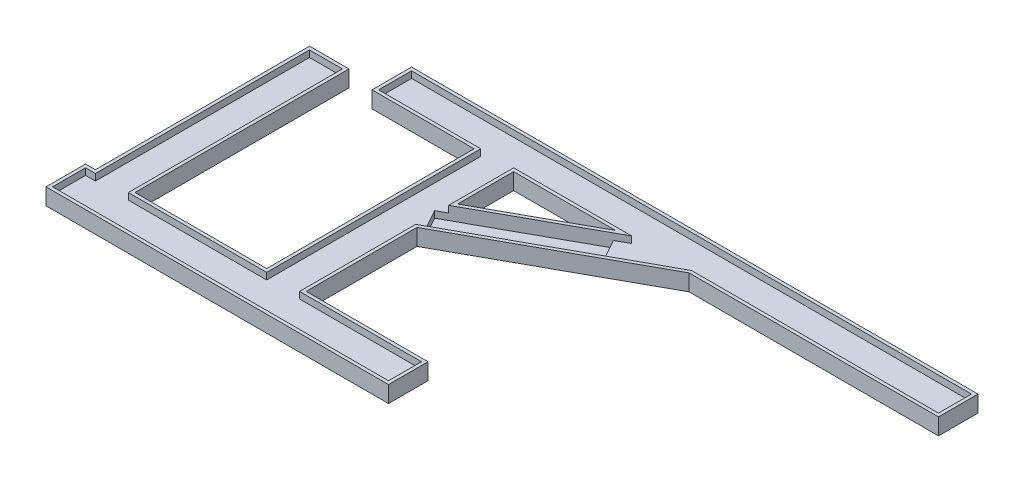
SolidWorks part; units mm, degrees
ref_plane "前视基准面" through (0, 0, 0) normal (0, 0, 1) x (1, 0, 0)
ref_plane "上视基准面" through (0, 0, 0) normal (0, 1, 0) x (1, 0, 0)
ref_plane "右视基准面" through (0, 0, 0) normal (1, 0, 0) x (0, 0, -1)
other "Configuration Table"
sketch "草图1" plane through (0, 0, 0) normal (0, 1, 0) x (1, 0, 0)
  line L0 (0, 0) -> (0, -75) construction
  line L1 (-42.5, -5) -> (42.5, -5)
  line L2 (-42.5, -5) -> (-42.5, 5)
  line L3 (-42.5, 5) -> (42.5, 5)
  line L4 (42.5, -5) -> (42.5, 5)
  line L5 (-42.5, -5) -> (42.5, 5) construction
  line L6 (-42.5, 5) -> (42.5, -5) construction
  line L7 (-25.5, -80) -> (25.5, -80)
  line L8 (-25.5, -80) -> (-25.5, -70)
  line L9 (-25.5, -70) -> (25.5, -70)
  line L10 (25.5, -80) -> (25.5, -70)
  line L11 (-25.5, -80) -> (25.5, -70) construction
  line L12 (-25.5, -70) -> (25.5, -80) construction
  line L13 (-11.5, -70) -> (-21.5, -70)
  line L18 (-11.5, -70) -> (-11.5, -5)
  line L19 (-11.5, -5) -> (-21.5, -5)
  line L20 (-21.5, -70) -> (-21.5, -5)
  line L21 (-11.5, -70) -> (-21.5, -5) construction
  line L22 (-11.5, -5) -> (-21.5, -70) construction
  line L28 (-76.5, -80) -> (-25.5, -80)
  line L33 (-76.5, -80) -> (-76.5, -70)
  line L35 (-16.5, -37.5) -> (-16.5, -32.5) construction
  line L44 (-16.5, -32.5) -> (42.5, 0)
  line L45 (-16.5, -37.5) -> (42.5, -5)
  line L46 (42.5, 5) -> (-16.5, -27.5)
  line L47 (-16.5, -27.5) -> (-16.5, -32.5)
  line L51 (-76.5, -70) -> (-25.5, -70)
  line L52 (-25.5, -80) -> (-25.5, -70)
  line L53 (-73.5, -70) -> (-63.5, -70)
  line L54 (-73.5, -70) -> (-73.5, -5)
  line L55 (-73.5, -5) -> (-63.5, -5)
  line L56 (-63.5, -70) -> (-63.5, -5)
  line L57 (-73.5, -70) -> (-63.5, -5) construction
  line L58 (-73.5, -5) -> (-63.5, -70) construction
  line L59 (-76.5, -80) -> (-25.5, -70) construction
  line L60 (-76.5, -70) -> (-25.5, -80) construction
  line L65 (127.5, -5) -> (42.5, -5)
  line L66 (127.5, -5) -> (127.5, 5)
  line L67 (127.5, 5) -> (42.5, 5)
  line L68 (42.5, -5) -> (42.5, 5)
  line L69 (127.5, -5) -> (42.5, 5) construction
  line L70 (127.5, 5) -> (42.5, -5) construction
  point P0 (0, 0)
  point P6 (0, -75)
  point P11 (-16.5, -37.5)
  point P16 (85, 0)
  point P17 (-68.5, -37.5)
  point P21 (-51, -75)
  point P26 (5.3976, -20.4378)
  dimension "D1" = 10
  dimension "D2" = 85
  dimension "D3" = 51
  dimension "D4" = 10
  dimension "D5" = 10
  dimension "D6" = 65
  dimension "D7" = 4
  dimension "D8" = 51
  dimension "D9" = 21
  dimension "D10" = 5
  dimension "D11" = 25
  dimension "D12" = 65
  dimension "D13" = 85
  dimension "D14" = 10
sketch "草图3" plane through (0, 0, 0) normal (0, 1, 0) x (1, 0, 0)
  line L0 (42.5, -5) -> (42.5, 5)
  line L1 (-73.5, -5) -> (-63.5, -5)
  line L2 (-73.5, -5) -> (-73.5, -70)
  line L3 (-73.5, -70) -> (-63.5, -70)
  line L4 (-63.5, -5) -> (-63.5, -70)
  line L5 (-76.5, -80) -> (25.5, -80)
  line L6 (-76.5, -80) -> (-76.5, -70)
  line L7 (-76.5, -70) -> (25.5, -70)
  line L8 (25.5, -80) -> (25.5, -70)
  line L9 (-21.5, -5) -> (-11.5, -5)
  line L10 (-21.5, -5) -> (-21.5, -70)
  line L11 (-21.5, -70) -> (-11.5, -70)
  line L12 (-11.5, -5) -> (-11.5, -70)
  line L13 (-42.5, 5) -> (127.5, 5)
  line L14 (-42.5, 5) -> (-42.5, -5)
  line L15 (-42.5, -5) -> (127.5, -5)
  line L16 (127.5, 5) -> (127.5, -5)
  line L17 (42.5, -5) -> (-16.5, -37.5)
  line L18 (42.5, 5) -> (-16.5, -27.5)
  line L19 (-16.5, -37.5) -> (-16.5, -27.5)
extrude "凸台-拉伸2" add sketch "草图3" along normal blind 1 contours L4 L1 L2 L3 | L5 L8 L7 L3 L6 | L17 L19 L18 L12 L9 L10 L7 | L18 L13 L14 L15 L9 | L16 L13 L0 L15 | L0 L18 L15 | L15 L18 L12 L17 | L19 L17 L12 L18
sketch "草图4" plane through (0, 1, 0) normal (0, 1, 0) x (1, 0, 0)
  line L0 (-10.5, -35.3366) -> (42.7572, -6)
  line L1 (42.7572, -6) -> (128.5, -6)
  line L2 (128.5, -6) -> (128.5, 6)
  line L3 (128.5, 6) -> (-43.5, 6)
  line L4 (-43.5, 6) -> (-43.5, -6)
  line L5 (-43.5, -6) -> (-22.5, -6)
  line L6 (-22.5, -6) -> (-22.5, -69)
  line L7 (-22.5, -69) -> (-62.5, -69)
  line L8 (-62.5, -69) -> (-62.5, -4)
  line L9 (-62.5, -4) -> (-74.5, -4)
  line L10 (-74.5, -4) -> (-74.5, -69)
  line L11 (-74.5, -69) -> (-77.5, -69)
  line L12 (-77.5, -69) -> (-77.5, -81)
  line L13 (-77.5, -81) -> (26.5, -81)
  line L14 (26.5, -81) -> (26.5, -69)
  line L15 (26.5, -69) -> (-10.5, -69)
  line L16 (-10.5, -69) -> (-10.5, -35.3366)
  line L17 (-11.5, -34.7458) -> (42.5, -5)
  line L18 (42.5, -5) -> (127.5, -5)
  line L19 (127.5, -5) -> (127.5, 5)
  line L20 (127.5, 5) -> (-42.5, 5)
  line L21 (-42.5, 5) -> (-42.5, -5)
  line L22 (-42.5, -5) -> (-21.5, -5)
  line L23 (-21.5, -5) -> (-21.5, -70)
  line L24 (-21.5, -70) -> (-63.5, -70)
  line L25 (-63.5, -70) -> (-63.5, -5)
  line L26 (-63.5, -5) -> (-73.5, -5)
  line L27 (-73.5, -5) -> (-73.5, -70)
  line L28 (-73.5, -70) -> (-76.5, -70)
  line L29 (-76.5, -70) -> (-76.5, -80)
  line L30 (-76.5, -80) -> (25.5, -80)
  line L31 (25.5, -80) -> (25.5, -70)
  line L32 (25.5, -70) -> (-11.5, -70)
  line L33 (-11.5, -70) -> (-11.5, -34.7458)
  line L34 (-11.5, -34.7458) -> (42.5, -5)
  line L35 (42.5, -5) -> (127.5, -5)
  line L36 (127.5, -5) -> (127.5, 5)
  line L37 (127.5, 5) -> (-42.5, 5)
  line L38 (-42.5, 5) -> (-42.5, -5)
  line L39 (-42.5, -5) -> (-21.5, -5)
  line L40 (-21.5, -5) -> (-21.5, -70)
  line L41 (-21.5, -70) -> (-63.5, -70)
  line L42 (-63.5, -70) -> (-63.5, -5)
  line L43 (-63.5, -5) -> (-73.5, -5)
  line L44 (-73.5, -5) -> (-73.5, -70)
  line L45 (-73.5, -70) -> (-76.5, -70)
  line L46 (-76.5, -70) -> (-76.5, -80)
  line L47 (-76.5, -80) -> (25.5, -80)
  line L48 (25.5, -80) -> (25.5, -70)
  line L49 (25.5, -70) -> (-11.5, -70)
  line L50 (-11.5, -70) -> (-11.5, -34.7458)
  line L51 (-11.5, -5) -> (-11.5, -24.7458)
  line L52 (-11.5, -24.7458) -> (24.3462, -5)
  line L53 (24.3462, -5) -> (-11.5, -5)
  line L54 (20.4582, -6) -> (-10.5, -6)
  line L55 (-10.5, -6) -> (-10.5, -23.0532)
  line L56 (-10.5, -23.0532) -> (20.4582, -6)
  line M21 (-11.5, -34.7458) -> (42.5, -5)
  line M22 (42.5, -5) -> (127.5, -5)
  line M23 (127.5, -5) -> (127.5, 5)
  line M24 (127.5, 5) -> (-42.5, 5)
  line M25 (-42.5, 5) -> (-42.5, -5)
  line M26 (-42.5, -5) -> (-21.5, -5)
  line M27 (-21.5, -5) -> (-21.5, -70)
  line M28 (-21.5, -70) -> (-63.5, -70)
  line M29 (-63.5, -70) -> (-63.5, -5)
  line M30 (-63.5, -5) -> (-73.5, -5)
  line M31 (-73.5, -5) -> (-73.5, -70)
  line M32 (-73.5, -70) -> (-76.5, -70)
  line M33 (-76.5, -70) -> (-76.5, -80)
  line M34 (-76.5, -80) -> (25.5, -80)
  line M35 (25.5, -80) -> (25.5, -70)
  line M36 (25.5, -70) -> (-11.5, -70)
  line M37 (-11.5, -70) -> (-11.5, -34.7458)
  line M38 (-11.5, -5) -> (24.3462, -5)
  line M39 (24.3462, -5) -> (-11.5, -24.7458)
  line M40 (-11.5, -24.7458) -> (-11.5, -5)
  dimension "D1" = 0
  dimension "D2" = 1
  dimension "D3" = 1
extrude "凸台-拉伸3" add sketch "草图4" along normal blind 4 and the other way blind 1 contours L15 L16 L0 L1 L2 L3 L4 L5 L6 L7 L8 L9 L10 L11 L12 L13 L14 M21 M37 M36 M35 M34 M33 M32 M31 M30 M29 M28 M27 M26 M25 M24 M23 M22 | L56 L55 L54 M38 M40 M39
sketch "草图5" plane through (0, 1, 0) normal (0, 1, 0) x (1, 0, 0)
  line L0 (-14.2336, -26.2515) -> (-10.0074, -33.9236)
  line L1 (42.5, 5) -> (-16.5, -27.5) construction
  line L2 (-16.5, -37.5) -> (42.5, -5) construction
  line L3 (20.8025, -6.952) -> (25.0287, -14.624)
  line L4 (-11.5, -5) -> (-11.5, -24.7458)
  line L5 (-11.5, -24.7458) -> (24.3462, -5)
  line L6 (24.3462, -5) -> (-11.5, -5)
  line L8 (-14.2336, -26.2515) -> (-11.5, -24.7458)
  line L21 (-11.5, -34.7458) -> (42.5, -5)
  line L22 (42.5, -5) -> (127.5, -5)
  line L23 (127.5, -5) -> (127.5, 5)
  line L24 (127.5, 5) -> (-42.5, 5)
  line L25 (-42.5, 5) -> (-42.5, -5)
  line L26 (-42.5, -5) -> (-21.5, -5)
  line L27 (-21.5, -5) -> (-21.5, -70)
  line L28 (-21.5, -70) -> (-63.5, -70)
  line L29 (-63.5, -70) -> (-63.5, -5)
  line L30 (-63.5, -5) -> (-73.5, -5)
  line L31 (-73.5, -5) -> (-73.5, -70)
  line L32 (-73.5, -70) -> (-76.5, -70)
  line L33 (-76.5, -70) -> (-76.5, -80)
  line L34 (-76.5, -80) -> (25.5, -80)
  line L35 (25.5, -80) -> (25.5, -70)
  line L36 (25.5, -70) -> (-11.5, -70)
  line L37 (-11.5, -70) -> (-11.5, -34.7458)
  line L38 (-11.5, -34.7458) -> (42.5, -5)
  line L39 (42.5, -5) -> (127.5, -5)
  line L40 (127.5, -5) -> (127.5, 5)
  line L41 (127.5, 5) -> (-42.5, 5)
  line L42 (-42.5, 5) -> (-42.5, -5)
  line L43 (-42.5, -5) -> (-21.5, -5)
  line L44 (-21.5, -5) -> (-21.5, -70)
  line L45 (-21.5, -70) -> (-63.5, -70)
  line L46 (-63.5, -70) -> (-63.5, -5)
  line L47 (-63.5, -5) -> (-73.5, -5)
  line L48 (-73.5, -5) -> (-73.5, -70)
  line L49 (-73.5, -70) -> (-76.5, -70)
  line L50 (-76.5, -70) -> (-76.5, -80)
  line L51 (-76.5, -80) -> (25.5, -80)
  line L52 (25.5, -80) -> (25.5, -70)
  line L53 (25.5, -70) -> (-11.5, -70)
  line L54 (-11.5, -70) -> (-11.5, -34.7458)
  line M21 (-11.5, -34.7458) -> (42.5, -5)
  line M22 (42.5, -5) -> (127.5, -5)
  line M23 (127.5, -5) -> (127.5, 5)
  line M24 (127.5, 5) -> (-42.5, 5)
  line M25 (-42.5, 5) -> (-42.5, -5)
  line M26 (-42.5, -5) -> (-21.5, -5)
  line M27 (-21.5, -5) -> (-21.5, -70)
  line M28 (-21.5, -70) -> (-63.5, -70)
  line M29 (-63.5, -70) -> (-63.5, -5)
  line M30 (-63.5, -5) -> (-73.5, -5)
  line M31 (-73.5, -5) -> (-73.5, -70)
  line M32 (-73.5, -70) -> (-76.5, -70)
  line M33 (-76.5, -70) -> (-76.5, -80)
  line M34 (-76.5, -80) -> (25.5, -80)
  line M35 (25.5, -80) -> (25.5, -70)
  line M36 (25.5, -70) -> (-11.5, -70)
  line M37 (-11.5, -70) -> (-11.5, -34.7458)
  line M38 (-11.5, -5) -> (24.3462, -5)
  line M39 (24.3462, -5) -> (-11.5, -24.7458)
  line M40 (-11.5, -24.7458) -> (-11.5, -5)
  dimension "D2" = 20
  dimension "D3" = 20
  dimension "D1" = 0
extrude "凸台-拉伸4" add sketch "草图5" along normal blind 2 contours L0 L8 L3 M40 M38 M39 M21 M22 M23 M24 M25 M26 M27 M28 M29 M30 M31 M32 M33 M34 M35 M36 M37
sketch "草图7" plane through (0, 5, 0) normal (0, 1, 0) x (1, 0, 0)
  line L0 (128.5, 6) -> (-43.5, 6) construction
  line L1 (128.5, -6) -> (118.5, -6)
  line L2 (128.5, -6) -> (128.5, 6)
  line L3 (128.5, 6) -> (118.5, 6)
  line L4 (118.5, -6) -> (118.5, 6)
  dimension "D1" = 10
extrude "切除-拉伸1" cut sketch "草图7" against normal blind 5
sketch "草图8" plane through (0, 3, 0) normal (0, 1, 0) x (1, 0, 0)
  line L0 (127.5, -5) -> (42.5, -5) construction
  line L1 (118.5, 5) -> (117.5, 5)
  line L2 (118.5, 5) -> (118.5, -5)
  line L3 (118.5, -5) -> (117.5, -5)
  line L4 (117.5, 5) -> (117.5, -5)
  dimension "D1" = 1
extrude "凸台-拉伸5" add sketch "草图8" along normal blind 2
sketch "草图9" plane through (0, 5, 0) normal (0, 1, 0) x (1, 0, 0)
  line L0 (-43.5, -6) -> (-22.5, -6) construction
  line L1 (-43.5, 6) -> (-53.5, 6)
  line L2 (-43.5, 6) -> (-43.5, -6)
  line L3 (-43.5, -6) -> (-53.5, -6)
  line L4 (-53.5, 6) -> (-53.5, -6)
  dimension "D1" = 10
extrude "凸台-拉伸7" add sketch "草图9" against normal blind 5
sketch "草图10" plane through (0, 5, 0) normal (0, 1, 0) x (1, 0, 0)
  line L0 (-42.5, -5) -> (42.5, -5) construction
  line L1 (-42.5, 5) -> (-52.5, 5)
  line L2 (-42.5, 5) -> (-42.5, -5)
  line L3 (-42.5, -5) -> (-52.5, -5)
  line L4 (-52.5, 5) -> (-52.5, -5)
  dimension "D1" = 10
extrude "切除-拉伸2" cut sketch "草图10" against normal blind 2
